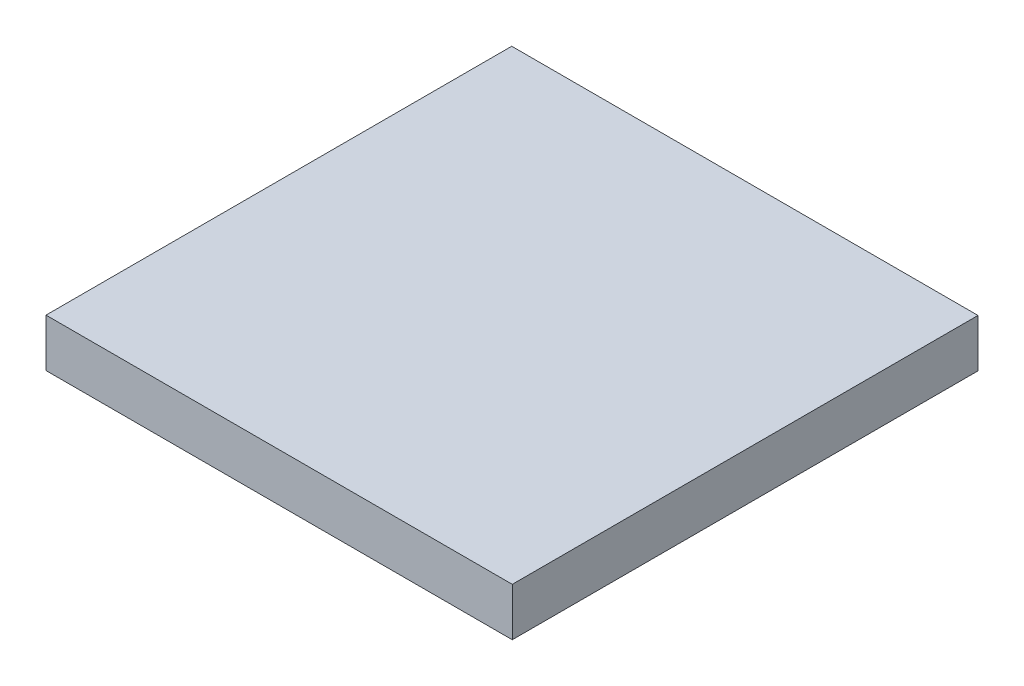
SolidWorks part; units mm, degrees
material "CA"
ref_plane "Front Plane" through (0, 0, 0) normal (0, 0, 1) x (1, 0, 0)
ref_plane "Top Plane" through (0, 0, 0) normal (0, 1, 0) x (1, 0, 0)
ref_plane "Right Plane" through (0, 0, 0) normal (1, 0, 0) x (0, 0, -1)
sketch "Sketch1" plane through (0, 0, 0) normal (0, 1, 0) x (1, 0, 0)
  line L1 (0, 0) -> (127.9906, 0)
  line L2 (0, 0) -> (0, 127.8382)
  line L3 (0, 127.8382) -> (127.9906, 127.8382)
  line L4 (127.9906, 0) -> (127.9906, 127.8382)
  dimension "D1" = 127.9906
  dimension "D2" = 127.8382
extrude "Boss-Extrude1" add sketch "Sketch1" along normal blind 13.1826
sketch "Sketch2" plane through (0, 0, 0) normal (0, -1, 0) x (1, 0, 0)
  line L0 (0, -127.8382) -> (0, 0) construction
  line L1 (12.7, -12.7) -> (115.2906, -12.7)
  line L2 (12.7, -12.7) -> (12.7, -115.1382)
  line L3 (12.7, -115.1382) -> (115.2906, -115.1382)
  line L4 (115.2906, -12.7) -> (115.2906, -115.1382)
  line L5 (127.9906, 0) -> (127.9906, -127.8382) construction
  line L6 (0, 0) -> (127.9906, 0) construction
  line L7 (127.9906, -127.8382) -> (0, -127.8382) construction
  dimension "D1" = 12.7
  dimension "D2" = 12.7
  dimension "D3" = 12.7
  dimension "D4" = 12.7
extrude "Cut-Extrude1" cut sketch "Sketch2" against normal blind 7.874
sketch "Sketch3" plane through (0, 0, 0) normal (0, -1, 0) x (1, 0, 0)
  line L0 (0, -63.9191) -> (127.9906, -63.9191) construction
  line L1 (0, -127.8382) -> (0, 0) construction
  line L2 (127.9906, 0) -> (127.9906, -127.8382) construction
  line L3 (12.7, -12.7) -> (12.7, -115.1382) construction
  line L4 (127.9906, -127.8382) -> (0, -127.8382) construction
  line L5 (63.9953, 0) -> (63.9953, -127.8382) construction
  line L6 (0, 0) -> (127.9906, 0) construction
  circle A0 centre (8.255, -108.7882) radius 1.27
  circle A1 centre (8.255, -19.05) radius 1.27
  circle A2 centre (119.7356, -108.7882) radius 1.27
  circle A3 centre (119.7356, -19.05) radius 1.27
  dimension "D1" = 2.54
  dimension "D2" = 4.445
  dimension "D3" = 19.05
extrude "Cut-Extrude2" cut sketch "Sketch3" against normal blind 7.874
sketch "Sketch4" plane through (0, 7.874, 0) normal (0, -1, 0) x (-1, 0, 0)
  line L0 (-12.7, 115.1382) -> (-115.2906, 115.1382) construction
  line L1 (-34.5694, 68.8594) -> (-50.3682, 68.8594)
  line L2 (-34.5694, 68.8594) -> (-34.5694, 77.1398)
  line L3 (-34.5694, 77.1398) -> (-50.3682, 77.1398)
  line L4 (-50.3682, 68.8594) -> (-50.3682, 77.1398)
  line L5 (-12.7, 12.7) -> (-12.7, 115.1382) construction
  dimension "D1" = 15.7988
  dimension "D2" = 8.2804
  dimension "D3" = 37.9984
  dimension "D4" = 21.8694
extrude "Boss-Extrude2" add sketch "Sketch4" along normal blind 9.8298
sketch "Sketch5" plane through (0, 7.874, 0) normal (0, -1, 0) x (-1, 0, 0)
  line L0 (-12.7, 12.7) -> (-12.7, 115.1382) construction
  line L1 (-13.2842, 51.9684) -> (-22.1742, 51.9684)
  line L2 (-13.2842, 51.9684) -> (-13.2842, 79.9084)
  line L3 (-13.2842, 79.9084) -> (-22.1742, 79.9084)
  line L4 (-22.1742, 51.9684) -> (-22.1742, 79.9084)
  line L5 (-12.7, 115.1382) -> (-115.2906, 115.1382) construction
  line L6 (-63.9953, 12.7) -> (-63.9953, 115.1382) construction
  line L7 (-115.2906, 12.7) -> (-12.7, 12.7) construction
  line L8 (-12.7, 115.1382) -> (-115.2906, 115.1382) construction
  line L9 (-114.7064, 79.9084) -> (-105.8164, 79.9084)
  line L10 (-105.8164, 51.9684) -> (-105.8164, 79.9084)
  line L11 (-114.7064, 51.9684) -> (-105.8164, 51.9684)
  line L12 (-114.7064, 51.9684) -> (-114.7064, 79.9084)
  point P4 (-12.7, 63.9191)
  dimension "D1" = 8.89
  dimension "D2" = 27.94
  dimension "D3" = 0.5842
  dimension "D4" = 35.2298
extrude "Boss-Extrude3" add sketch "Sketch5" along normal blind 7.874
sketch "Sketch6" plane through (0, 0, 0) normal (0, -1, 0) x (-1, 0, 0)
  line L0 (-12.7, 115.1382) -> (-115.2906, 115.1382) construction
  line L1 (-12.7, 12.7) -> (-12.7, 115.1382) construction
  line L2 (0, 63.9191) -> (-127.9906, 63.9191) construction
  line L3 (0, 127.8382) -> (0, 0) construction
  line L4 (-127.9906, 0) -> (-127.9906, 127.8382) construction
  line L5 (-63.9953, 127.8382) -> (-63.9953, 0) construction
  line L6 (-127.9906, 127.8382) -> (0, 127.8382) construction
  line L7 (0, 0) -> (-127.9906, 0) construction
  circle A0 centre (-23.4823, 118.7323) radius 1.5113
  circle A1 centre (-104.5083, 118.7323) radius 1.5113 construction
  circle A2 centre (-104.5083, 9.1059) radius 1.5113
  dimension "D1" = 3.0226
  dimension "D2" = 3.5941
  dimension "D3" = 10.7823
extrude "Boss-Extrude4" add sketch "Sketch6" along normal blind 3.683
fillet "Fillet3" radius 1.27 1 edges at (12.7, 3.937, -115.1382)
fillet "Fillet4" radius 1.27 1 edges at (12.7, 3.937, -12.7)
fillet "Fillet5" radius 1.27 1 edges at (115.2906, 3.937, -12.7)
fillet "Fillet6" radius 1.27 1 edges at (115.2906, 3.937, -115.1382)
fillet "Fillet8" radius 1.27 1 edges at (23.4823, -3.683, -120.2436)
fillet "Fillet9" radius 1.27 1 edges at (104.5083, -3.683, -10.6172)
